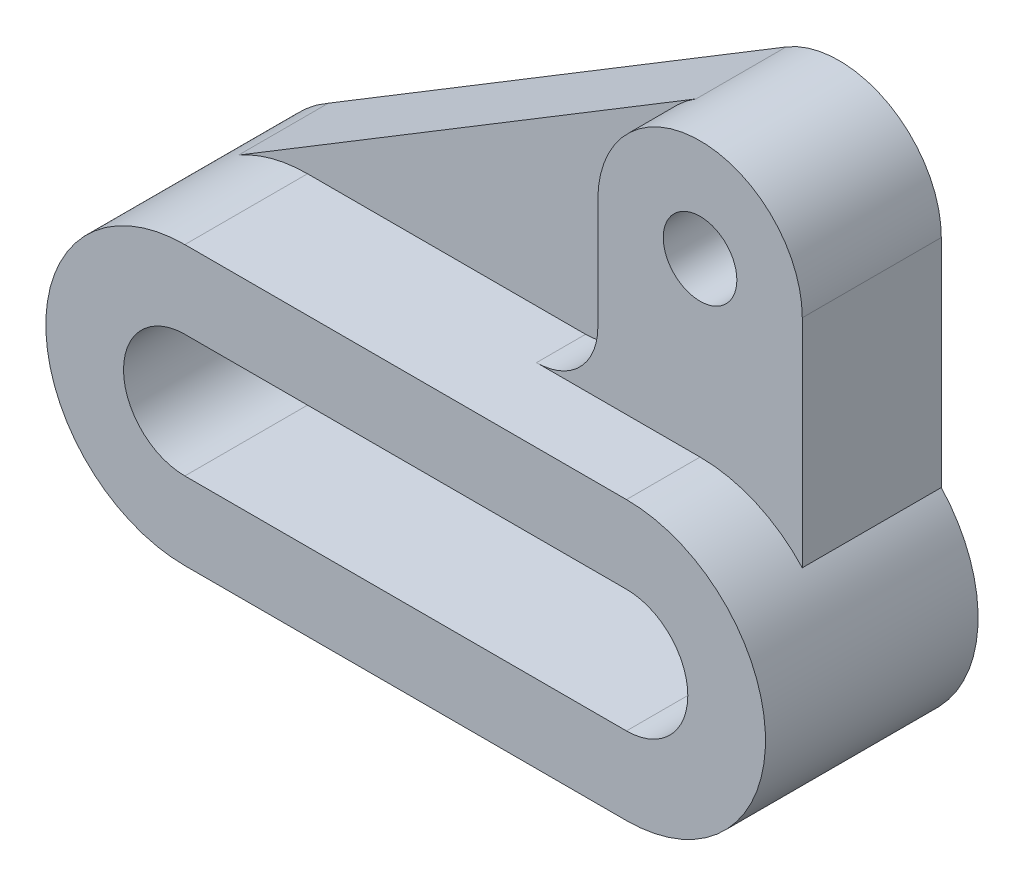
SolidWorks part; units mm, degrees
ref_plane "정면" through (0, 0, 0) normal (0, 0, 1) x (1, 0, 0)
ref_plane "평면" through (0, 0, 0) normal (0, 1, 0) x (1, 0, 0)
ref_plane "우측면" through (0, 0, 0) normal (1, 0, 0) x (0, 0, -1)
sketch "스케치1" plane through (0, 0, 0) normal (0, 0, 1) x (1, 0, 0)
  line L8 (0, 15) -> (108, 15)
  line L9 (0, -15) -> (108, -15)
  line L10 (0, 34) -> (108, 34)
  line L11 (0, -34) -> (108, -34)
  arc A8 (0, 15) -> (0, -15) centre (0, 0) ccw
  arc A9 (108, -15) -> (108, 15) centre (108, 0) ccw
  arc A10 (0, 34) -> (0, -34) centre (0, 0) ccw
  arc A11 (108, -34) -> (108, 34) centre (108, 0) ccw
  dimension "D1" = 15
  dimension "D2" = 108
  dimension "D3" = 34
extrude "보스-돌출1" add sketch "스케치1" along normal blind 52
sketch "스케치2" plane through (0, 0, 0) normal (0, 0, 1) x (1, 0, 0)
  line L1 (108, 34) -> (0, 34) construction
  line L2 (108, 34) -> (68, 34)
  line L3 (83, 76) -> (83, 49)
  line L4 (133, 76) -> (133, 23.0434)
  circle A0 centre (108, 76) radius 9
  arc A1 (133, 76) -> (83, 76) centre (108, 76) ccw
  arc A2 (108, -34) -> (108, 34) centre (108, 0) ccw construction
  arc A3 (133, 23.0434) -> (108, 34) centre (108, 0) ccw
  arc A4 (68, 34) -> (83, 49) centre (68, 49) ccw
  dimension "D1" = 15
  dimension "D2" = 18
  dimension "D4" = 25
  dimension "D3" = 76
  dimension "D5" = 108
extrude "보스-돌출2" add sketch "스케치2" along normal blind 34
sketch "스케치3" plane through (0, 0, 0) normal (0, 0, 1) x (1, 0, 0)
  line L0 (-16.8912, 29.5074) -> (95.0377, 97.3771)
  line L1 (108, 34) -> (0, 34) construction
  line L2 (83, 76) -> (83, 49) construction
  line L3 (68, 34) -> (0, 34)
  line L4 (83, 76) -> (83, 49)
  arc A3 (0, 34) -> (0, -34) centre (0, 0) ccw construction
  arc A4 (133, 76) -> (83, 76) centre (108, 76) ccw construction
  arc A5 (0, 34) -> (-16.8912, 29.5074) centre (0, 0) ccw
  arc A6 (68, 34) -> (83, 49) centre (68, 49) ccw construction
  arc A7 (95.0377, 97.3771) -> (83, 76) centre (108, 76) ccw
  arc A8 (68, 34) -> (83, 49) centre (68, 49) ccw
  dimension "D1" = 95.0377
  dimension "D2" = 16.8912
extrude "보스-돌출3" add sketch "스케치3" along normal blind 22
